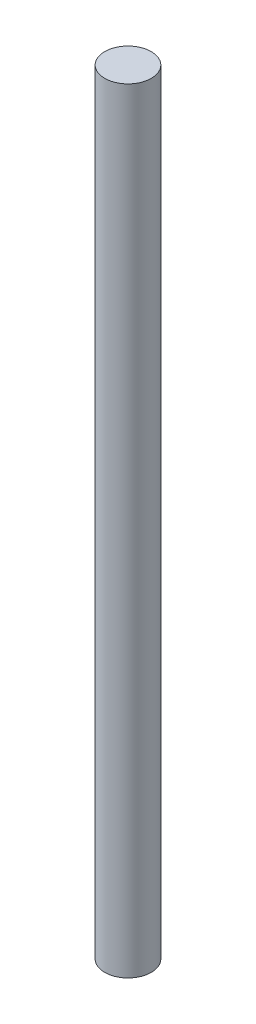
SolidWorks part; units mm, degrees
ref_plane "Front Plane" through (0, 0, 0) normal (0, 0, 1) x (1, 0, 0)
ref_plane "Top Plane" through (0, 0, 0) normal (0, 1, 0) x (1, 0, 0)
ref_plane "Right Plane" through (0, 0, 0) normal (1, 0, 0) x (0, 0, -1)
sketch "Sketch1" plane through (0, 0, 0) normal (0, 1, 0) x (1, 0, 0)
  circle A0 centre (0, 0) radius 0.3
extrude "Boss-Extrude1" add sketch "Sketch1" along normal blind 10
